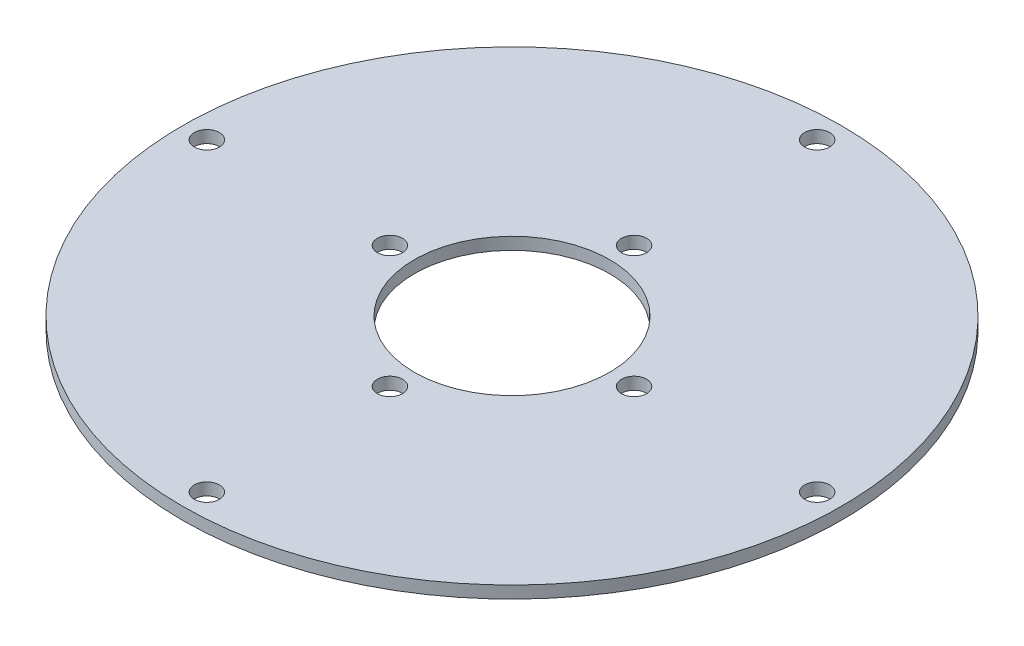
SolidWorks part; units mm, degrees
ref_plane "Front Plane" through (0, 0, 0) normal (0, 0, 1) x (1, 0, 0)
ref_plane "Top Plane" through (0, 0, 0) normal (0, 1, 0) x (1, 0, 0)
ref_plane "Right Plane" through (0, 0, 0) normal (1, 0, 0) x (0, 0, -1)
sketch "Sketch1" plane through (0, 0, 0) normal (0, 1, 0) x (1, 0, 0)
  line L0 (0, 85.725) -> (0, -85.725) construction
  line L1 (85.725, 0) -> (-85.725, 0) construction
  circle A0 centre (0, 0) radius 85.725
  circle A1 centre (0, 0) radius 25.4
  circle A2 centre (0, 0) radius 79.375 construction
  circle A3 centre (0, 79.375) radius 3.2639
  circle A4 centre (79.375, 0) radius 3.2639
  circle A5 centre (0, -79.375) radius 3.2639
  circle A6 centre (-79.375, 0) radius 3.2639
  circle A7 centre (0, 0) radius 31.75 construction
  circle A8 centre (0, 31.75) radius 3.2639
  circle A9 centre (31.75, 0) radius 3.2639
  circle A10 centre (0, -31.75) radius 3.2639
  circle A11 centre (-31.75, 0) radius 3.2639
  point P20 (0, 0)
  point P30 (0, 0)
  dimension "D1" = 171.45
  dimension "D2" = 50.8
  dimension "D3" = 158.75
  dimension "D4" = 6.5278
  dimension "D6" = 31.75
  dimension "D7" = 6.5278
  dimension "D5" = 4
  dimension "D8" = 4
extrude "Boss-Extrude1" add sketch "Sketch1" along normal blind 3.175
